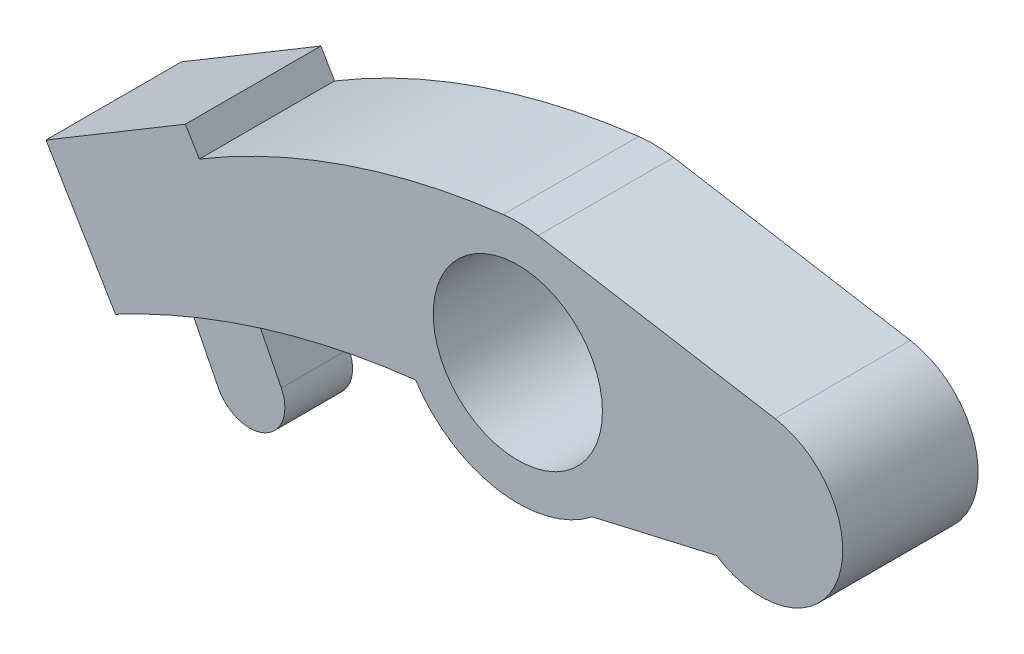
SolidWorks part; units mm, degrees
ref_plane "Front Plane" through (0, 0, 0) normal (0, 0, 1) x (1, 0, 0)
ref_plane "Top Plane" through (0, 0, 0) normal (0, 1, 0) x (1, 0, 0)
ref_plane "Right Plane" through (0, 0, 0) normal (1, 0, 0) x (0, 0, -1)
sketch "Sketch1" plane through (0, 0, 0) normal (0, 0, 1) x (1, 0, 0)
  line L0 (19, 5.9161) -> (0, 9.1277)
  line L1 (0, 0) -> (8.0512, 0) construction
  line L2 (18, 0) -> (32.1791, 0) construction
  line L3 (14.6834, -5) -> (5.5069, -7.1185)
  line L4 (-23.5301, 1.2569) -> (-24.557, 2.9731)
  line L5 (-24.557, 2.9731) -> (-34.8545, -3.1883)
  line L6 (-34.8545, -3.1883) -> (-29.72, -11.7695)
  arc A3 (1.5, 8.8741) -> (-1.0756, 8.9355) centre (0, 0) ccw
  circle A4 centre (0, 0) radius 6.25
  arc A5 (14.6834, -5) -> (19, 5.9161) centre (18, 0) ccw
  arc A6 (-1.0756, 8.9355) -> (-23.5301, 1.2569) centre (5.7364, -47.656) ccw
  arc A7 (-29.72, -11.7695) -> (-7.556, -4.8895) centre (-0.5823, -66.496) cw
  arc A8 (-7.556, -4.8895) -> (5.5069, -7.1185) centre (0, 0) ccw
  point P18 (-6.817, -5.8761)
  point P20 (-24.3598, 1.4198)
  point P21 (-23.1721, -1.1265)
  point P22 (0, 0)
  point P23 (-23.6508, 1.2915)
  point P24 (-7.556, -5)
  point P25 (-23.5301, 1.2569)
  dimension "D1" = 18
  dimension "D2" = 12.5
  dimension "D4" = 18
  dimension "D3" = 12
  dimension "D7" = 35
  dimension "D8" = 57
  dimension "D11" = 62
  dimension "D5" = 5
  dimension "D6" = 13
  dimension "D9" = 12
  dimension "D10" = 10
  dimension "D12" = 29.72
  dimension "D13" = 2
extrude "Boss-Extrude1" add sketch "Sketch1" along normal mid plane 10 contours A7 A8 L3 A5 L0 A3 A6 L4 L5 L6 A4
sketch "Sketch2" plane through (0, 0, 0) normal (0, 0, 1) x (1, 0, 0)
  line L0 (-29.72, -11.7695) -> (-27.0143, -10.4126)
  line L1 (-27.0143, -10.4126) -> (-24.6493, -15.1286)
  line L3 (-19.9705, -12.8595) -> (-22.2217, -8.3949)
  line L9 (5.5069, -7.1185) -> (14.6834, -5)
  line L10 (19, 5.9161) -> (1.5, 8.8741)
  line L11 (-23.5301, 1.2569) -> (-24.557, 2.9731)
  line L12 (-24.557, 2.9731) -> (-34.8545, -3.1883)
  line L13 (-34.8545, -3.1883) -> (-29.72, -11.7695)
  arc A0 (-7.556, -4.8895) -> (-29.72, -11.7695) centre (-0.5823, -66.496) ccw construction
  arc A1 (-24.6493, -15.1286) -> (-19.9705, -12.8595) centre (-22.3099, -13.994) ccw
  arc A6 (-7.556, -4.8895) -> (-29.72, -11.7695) centre (-0.5823, -66.496) ccw
  arc A7 (-7.556, -4.8895) -> (5.5069, -7.1185) centre (0, 0) ccw
  arc A8 (14.6834, -5) -> (19, 5.9161) centre (18, 0) ccw
  arc A9 (1.5, 8.8741) -> (-1.0756, 8.9355) centre (0, 0) ccw
  arc A10 (-1.0756, 8.9355) -> (-23.5301, 1.2569) centre (5.7364, -47.656) ccw
  arc A11 (-22.2217, -8.3949) -> (-29.72, -11.7695) centre (-0.5823, -66.496) ccw
  dimension "D1" = 5
  dimension "D2" = 0
extrude "Boss-Extrude2" add sketch "Sketch2" along normal mid plane 5 contours L3 A11 L1 A1
